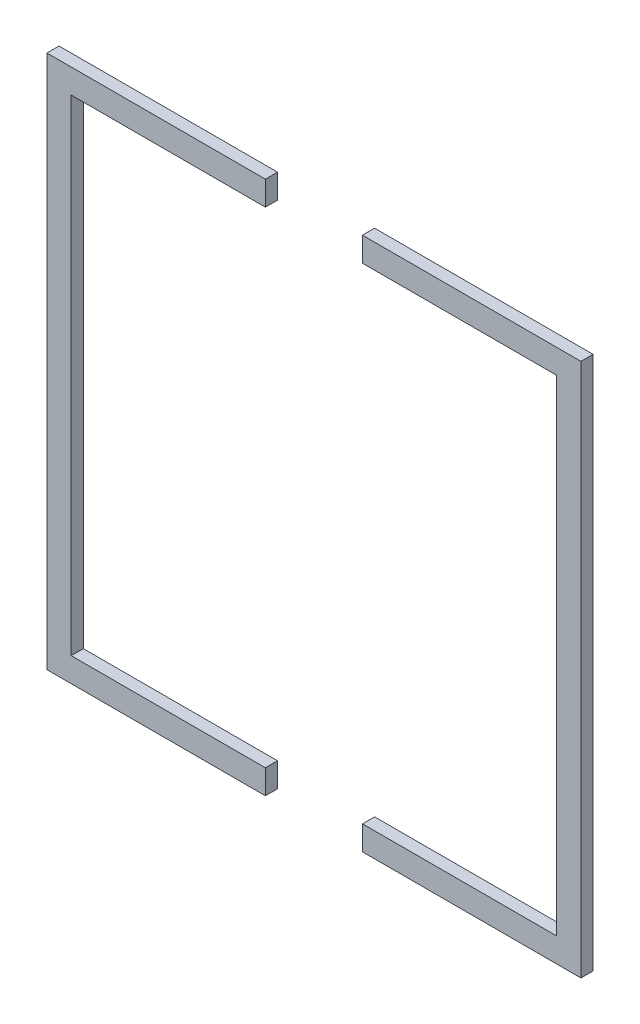
SolidWorks part; units mm, degrees
ref_plane "Front Plane" through (0, 0, 0) normal (0, 0, 1) x (1, 0, 0)
ref_plane "Top Plane" through (0, 0, 0) normal (0, 1, 0) x (1, 0, 0)
ref_plane "Right Plane" through (0, 0, 0) normal (1, 0, 0) x (0, 0, -1)
sketch "Sketch1" plane through (0, 0, 0) normal (0, 0, 1) x (1, 0, 0)
  line L0 (57.15, 6.35) -> (57.15, 0)
  line L1 (0, 0) -> (57.15, 0)
  line L2 (0, 0) -> (0, 139.7)
  line L3 (82.55, 0) -> (139.7, 0)
  line L4 (139.7, 0) -> (139.7, 139.7)
  line L5 (57.15, 139.7) -> (57.15, 133.35)
  line L6 (6.35, 133.35) -> (6.35, 6.35)
  line L7 (6.35, 6.35) -> (57.15, 6.35)
  line L8 (133.35, 133.35) -> (133.35, 6.35)
  line L9 (82.55, 6.35) -> (82.55, 0)
  line L10 (82.55, 133.35) -> (82.55, 139.7)
  line L11 (82.55, 133.35) -> (133.35, 133.35)
  line L12 (82.55, 139.7) -> (139.7, 139.7)
  line L13 (6.35, 133.35) -> (57.15, 133.35)
  line L14 (82.55, 6.35) -> (133.35, 6.35)
  line L15 (57.15, 139.7) -> (0, 139.7)
extrude "Boss-Extrude1" add sketch "Sketch1" along normal blind 3.175
